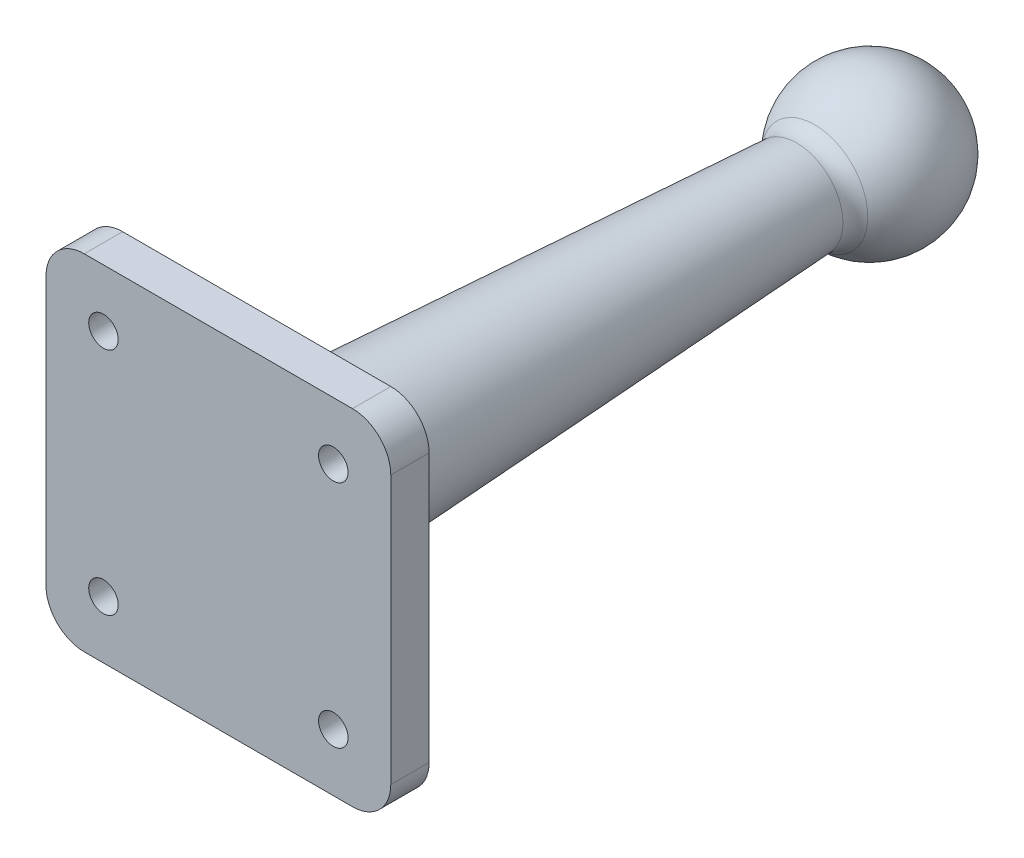
SolidWorks part; units mm, degrees
ref_plane "Front Plane" through (0, 0, 0) normal (0, 0, 1) x (1, 0, 0)
ref_plane "Top Plane" through (0, 0, 0) normal (0, 1, 0) x (1, 0, 0)
ref_plane "Right Plane" through (0, 0, 0) normal (1, 0, 0) x (0, 0, -1)
sketch "Sketch1" plane through (0, 0, 0) normal (0, 0, 1) x (1, 0, 0)
  line L1 (-22.5, -22.5) -> (22.5, -22.5)
  line L2 (-22.5, -22.5) -> (-22.5, 22.5)
  line L3 (-22.5, 22.5) -> (22.5, 22.5)
  line L4 (22.5, -22.5) -> (22.5, 22.5)
  line L5 (-22.5, -22.5) -> (22.5, 22.5) construction
  line L6 (-22.5, 22.5) -> (22.5, -22.5) construction
  point P0 (0, 0)
  dimension "D1" = 45
  dimension "D2" = 45
extrude "Boss-Extrude1" add sketch "Sketch1" along normal blind 5
fillet "Fillet1" radius 5 4 edges at (-22.5, -22.5, 2.5) (-22.5, 22.5, 2.5) (22.5, 22.5, 2.5) (22.5, -22.5, 2.5)
sketch "Sketch2" plane through (0, 0, 0) normal (0, 1, 0) x (1, 0, 0)
  line L0 (0, 0) -> (0, 16.8883) construction
  line L1 (17.5, 0) -> (-17.5, 0) construction
  line L2 (10, 0) -> (5.5, 80)
  line L3 (5.5, 80) -> (0, 80)
  line L5 (0, 80) -> (0, 0)
  line L6 (0, 0) -> (10, 0)
  dimension "D1" = 80
  dimension "D2" = 10
  dimension "D3" = 5.5
revolve "Revolve1" add sketch "Sketch2" angle 360 about L0
sketch "Sketch3" plane through (0, 0, 0) normal (0, 1, 0) x (1, 0, 0)
  line L0 (5.5, 80) -> (-5.5, 80) construction
  line L1 (0, 90) -> (0, 70)
  arc A0 (0, 70) -> (0, 90) centre (0, 80) ccw
  dimension "D1" = 20
revolve "Revolve2" add sketch "Sketch3" angle 360 about L1
sketch "Sketch4" plane through (0, 0, 0) normal (0, 0, -1) x (-1, 0, 0)
  line L0 (0, 22.5) -> (0, -22.5) construction
  line L1 (-17.5, 22.5) -> (17.5, 22.5) construction
  line L2 (17.5, -22.5) -> (-17.5, -22.5) construction
  line L3 (22.5, 0) -> (-22.5, 0) construction
  line L4 (22.5, 17.5) -> (22.5, -17.5) construction
  line L5 (-22.5, -17.5) -> (-22.5, 17.5) construction
  circle A0 centre (15, 15) radius 1.925
  circle A1 centre (15, -15) radius 1.925
  circle A2 centre (-15, -15) radius 1.925
  circle A3 centre (-15, 15) radius 1.925
  point P14 (0, 0)
  dimension "D1" = 3.85
  dimension "D3" = 15
  dimension "D2" = 15
extrude "Cut-Extrude1" cut sketch "Sketch4" against normal through all
fillet "Fillet3" radius 3 1 edges at (-5.952, 0, -71.9642)
chamfer "Chamfer1" distance 5 angle 45 1 edges at (10, 0, 0)
equation "\"D2@Sketch1\"=\"D1@Sketch1\""
